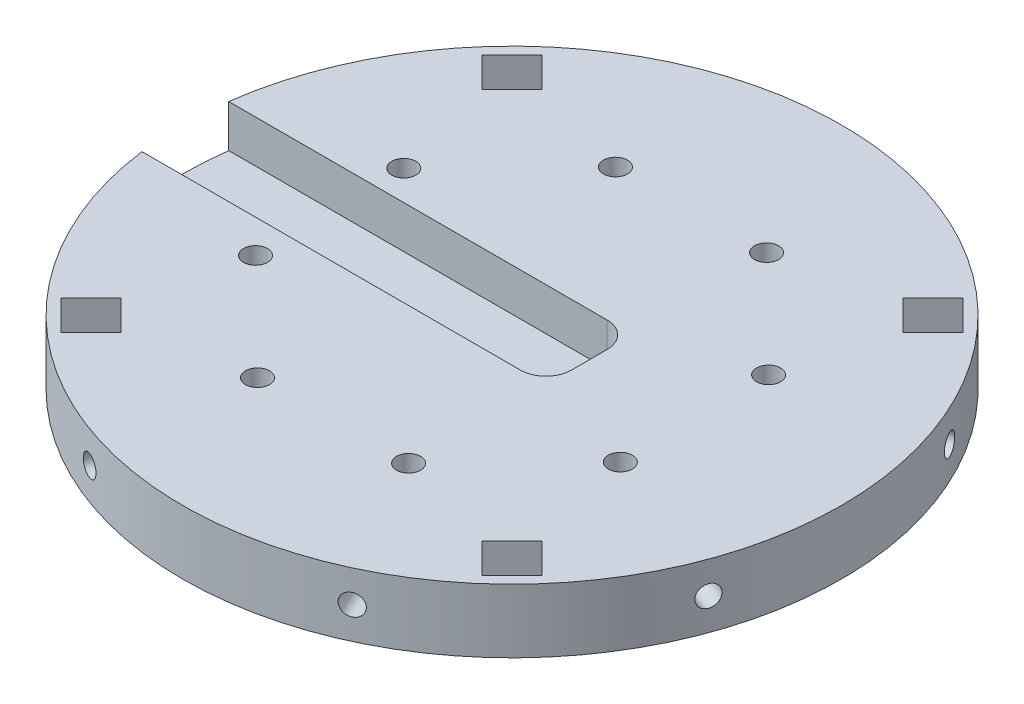
SolidWorks part; units mm, degrees
ref_plane "Front Plane" through (0, 0, 0) normal (0, 0, 1) x (1, 0, 0)
ref_plane "Top Plane" through (0, 0, 0) normal (0, 1, 0) x (1, 0, 0)
ref_plane "Right Plane" through (0, 0, 0) normal (1, 0, 0) x (0, 0, -1)
sketch "Sketch1" plane through (0, 0, 0) normal (0, 1, 0) x (1, 0, 0)
  circle A0 centre (0, 0) radius 98.425
  dimension "D1" = 196.85
extrude "Boss-Extrude1" add sketch "Sketch1" along normal blind 19.05
ref_plane "Plane1" through (0, 19.05, 0) normal (0, 1, 0) x (1, 0, 0)
sketch "Sketch2" plane through (0, 19.05, 0) normal (0, 1, 0) x (1, 0, 0)
  line L5 (0, 0) -> (59.5193, 0) construction
  line L9 (53.8815, 62.8618) -> (62.8618, 71.842)
  line L10 (0, 0) -> (139.194, 139.194) construction
  line L11 (53.8815, 62.8618) -> (62.8618, 53.8815)
  line L12 (62.8618, 71.842) -> (71.842, 62.8618)
  line L13 (62.8618, 53.8815) -> (71.842, 62.8618)
  line L14 (53.8815, 62.8618) -> (71.842, 62.8618) construction
  line L15 (62.8618, 71.842) -> (62.8618, 53.8815) construction
  circle A0 centre (0, 0) radius 88.9 construction
  point P0 (-88.8881, -1.4551)
  point P1 (62.8618, 62.8618)
  point P2 (0, 0)
  point P3 (62.8618, 62.8618)
  point P8 (67.5269, 46.1101)
  point P9 (62.8618, 62.8618)
  point P11 (62.8618, 62.8618)
  point P15 (71.761, 61.6577)
  dimension "D3" = 88.9
  dimension "7" = 177.8
  dimension "D1" = 12.7
  dimension "D2" = 12.7
  dimension "D5" = 0
  dimension "D6" = 0
  dimension "D7" = 45
sketch "Sketch3" plane through (0, 19.05, 0) normal (0, 1, 0) x (1, 0, 0)
  line L0 (0, 0) -> (-98.425, 0) construction
  circle A0 centre (0, 0) radius 66.675 construction
  circle A1 centre (0, 0) radius 58.42 construction
  circle A2 centre (-22.867, 53.7587) radius 3.5941
  circle A3 centre (0, 0) radius 98.425 construction
  point P6 (-58.42, 0)
  dimension "D1" = 133.35
  dimension "D2" = 116.84
  dimension "D3" = 7.1882
extrude "Cut-Extrude4" cut sketch "Sketch3" against normal up to next (19.05 mm away)
pattern_circular "CirPattern2" count 8 over 360 about axis through (0, 0, 0) along (0, 1, 0) of "Cut-Extrude4"
sketch "Sketch4" plane through (0, 19.05, 0) normal (0, 1, 0) x (1, 0, 0)
  line L0 (-97.5688, 12.954) -> (23.0812, 12.954)
  line L1 (23.0812, 12.954) -> (23.0812, -12.954)
  line L2 (23.0812, -12.954) -> (-97.5688, -12.954)
  circle A0 centre (0, 0) radius 98.425 construction
  circle A2 centre (-53.7587, -22.867) radius 3.5941 construction
  circle A3 centre (-21.8437, -54.1825) radius 3.5941 construction
  arc A4 (-97.5688, 12.954) -> (-97.5688, -12.954) centre (0, 0) ccw
  point P7 (-50.9978, -25.168)
  point P8 (-22.3521, -50.6246)
  point P15 (23.0812, 0)
  dimension "D1" = 25.908
  dimension "D3" = 120.65
extrude "Cut-Extrude5" cut sketch "Sketch4" against normal blind 12.7
extrude "Cut-Extrude7" cut sketch "Sketch2" against normal up to next (19.05 mm away)
pattern_circular "CirPattern4" count 4 over 360 about axis through (0, 0, 0) along (0, 1, 0) of "Cut-Extrude7"
ref_plane "Plane2" through (-33.6633, 0, 92.4892) normal (-0.342, 0, 0.9397) x (0, -1, 0)
sketch "Sketch5" plane through (-33.6633, 0, 92.4892) normal (-0.342, 0, 0.9397) x (0, -1, 0)
  circle A1 centre (-9.525, -0.1122) radius 3.175
  dimension "D1" = 6.35
  dimension "D2" = 9.525
extrude "Cut-Extrude8" cut sketch "Sketch5" against normal blind 12.7
pattern_circular "CirPattern5" count 8 over 360 about axis through (0, 0, 0) along (0, 1, 0) of "Cut-Extrude8"
fillet "Fillet1" radius 7.62 2 edges at (23.0812, 12.7, 12.954) (23.0812, 12.7, -12.954)
